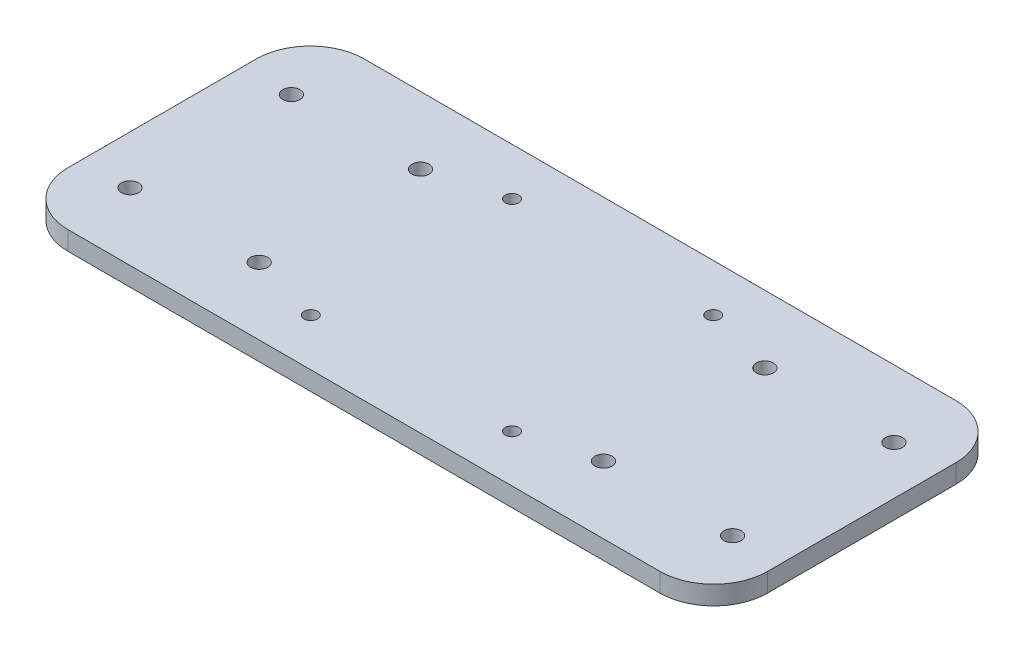
SolidWorks part; units mm, degrees
ref_plane "Front Plane" through (0, 0, 0) normal (0, 0, 1) x (1, 0, 0)
ref_plane "Top Plane" through (0, 0, 0) normal (0, 1, 0) x (1, 0, 0)
ref_plane "Right Plane" through (0, 0, 0) normal (1, 0, 0) x (0, 0, -1)
sketch "Sketch1" plane through (0, 0, 0) normal (0, 1, 0) x (1, 0, 0)
  line L0 (65, 20.185) -> (65, -51.1694) construction
  line L1 (0, 0) -> (130, 0)
  line L2 (0, 0) -> (0, -55)
  line L3 (0, -55) -> (130, -55)
  line L4 (130, 0) -> (130, -55)
  circle A0 centre (9, -12.5) radius 1.6
  circle A1 centre (9, -42.5) radius 1.6
  circle A2 centre (33, -12.5) radius 1.6
  circle A3 centre (33, -42.5) radius 1.6
  circle A4 centre (121, -42.5) radius 1.6
  circle A5 centre (97, -42.5) radius 1.6
  circle A6 centre (97, -12.5) radius 1.6
  circle A7 centre (121, -12.5) radius 1.6
  circle A8 centre (83.7, -8.8) radius 1.25
  circle A9 centre (83.7, -46.2) radius 1.25
  circle A10 centre (46.3, -46.2) radius 1.25
  circle A11 centre (46.3, -8.8) radius 1.25
  point P31 (0, 0)
  point P32 (0, 0)
  point P33 (0, 0)
  point P34 (0, 0)
  point P35 (0, 0)
  point P36 (0, 0)
  dimension "D3" = 3.2
  dimension "D4" = 3.2
  dimension "D5" = 3.2
  dimension "D6" = 3.2
  dimension "D13" = 2.5
  dimension "D14" = 2.5
  dimension "D15" = 2.5
  dimension "D16" = 2.5
  dimension "D1" = 130
  dimension "D2" = 55
  dimension "D7" = 30
  dimension "D8" = 24
  dimension "D9" = 30
  dimension "D10" = 24
  dimension "D11" = 12.5
  dimension "D12" = 9
  dimension "D17" = 18.7
  dimension "D18" = 37.4
  dimension "D19" = 37.4
  dimension "D20" = 37.4
  dimension "D21" = 18.7
  dimension "D22" = 18.7
  dimension "D23" = 18.7
  dimension "D24" = 8.8
extrude "Boss-Extrude1" add sketch "Sketch1" along normal blind 3.5
fillet "Fillet1" radius 10 4 edges at (0, 1.75, 55) (130, 1.75, 55) (130, 1.75, 0) (0, 1.75, 0)
